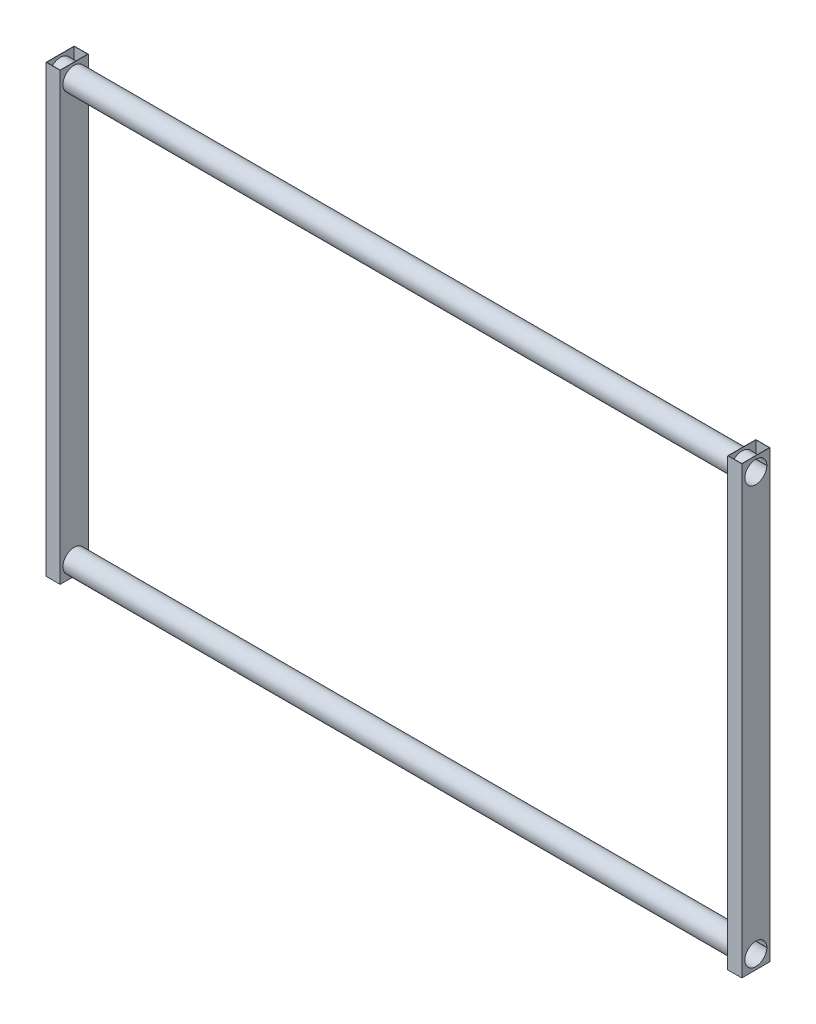
SolidWorks part; units mm, degrees
ref_plane "Front Plane" through (0, 0, 0) normal (0, 0, 1) x (1, 0, 0)
ref_plane "Top Plane" through (0, 0, 0) normal (0, 1, 0) x (1, 0, 0)
ref_plane "Right Plane" through (0, 0, 0) normal (1, 0, 0) x (0, 0, -1)
sketch "Sketch3" plane through (0, 0, 0) normal (0, 1, 0) x (1, 0, 0)
  line L0 (0, 209.8812) -> (0, -209.8812) construction
  line L2 (-209.8812, 0) -> (209.8812, 0) construction
  line L10 (2399, 209.8812) -> (2399, -209.8812) construction
  line L11 (1199.5, 209.8812) -> (1199.5, -209.8812) construction
  line L22 (-1, 49.5) -> (-49.5, 49.5)
  line L23 (0, 50.5) -> (-50.5, 50.5)
  line L24 (0, 50.5) -> (0, -50.5)
  line L25 (0, -50.5) -> (-50.5, -50.5)
  line L26 (-50.5, 50.5) -> (-50.5, -50.5)
  line L27 (-49.5, 49.5) -> (-49.5, -49.5)
  line L28 (-1, -49.5) -> (-49.5, -49.5)
  line L29 (-1, 49.5) -> (-1, -49.5)
  line L30 (2400, 49.5) -> (2400, -49.5)
  line L31 (2400, -49.5) -> (2448.5, -49.5)
  line L32 (2448.5, 49.5) -> (2448.5, -49.5)
  line L33 (2400, 49.5) -> (2448.5, 49.5)
  line L34 (2399, -50.5) -> (2449.5, -50.5)
  line L35 (2449.5, 50.5) -> (2449.5, -50.5)
  line L36 (2399, 50.5) -> (2449.5, 50.5)
  line L37 (2399, 50.5) -> (2399, -50.5)
  point P3 (0, 0)
  point P6 (0, 0)
  point P11 (0, 0)
  dimension "D1" = 101
  dimension "D2" = 50.5
  dimension "D3" = 1
  dimension "D7" = 2399
  dimension "D8" = 1199.5
extrude "Boss-Extrude1" add sketch "Sketch3" along normal blind 1600
sketch "Sketch4" plane through (2449.5, 0, 0) normal (1, 0, 0) x (0, 0, -1)
  circle A0 centre (0, 50) radius 39.5
  circle A1 centre (0, 1550) radius 39.5
  dimension "D1" = 79
  dimension "D3" = 79
  dimension "D2" = 50
  dimension "D4" = 1500
extrude "Cut-Extrude1" cut sketch "Sketch4" against normal up to surface (1 mm away) up to face at (2448.5, 800, 0)
sketch "Sketch5" plane through (-50.5, 0, 0) normal (-1, 0, 0) x (0, 0, 1)
  circle A0 centre (0, 50) radius 39.5
  circle A1 centre (0, 1550) radius 39.5
  dimension "D1" = 79
  dimension "D3" = 79
  dimension "D2" = 50
  dimension "D4" = 1500
extrude "Cut-Extrude2" cut sketch "Sketch5" against normal up to surface (1 mm away) up to face at (-49.5, 800, 0)
sketch "Sketch6" plane through (2400, 0, 0) normal (1, 0, 0) x (0, 0, -1)
  circle A0 centre (0, 50) radius 40.5
  circle A1 centre (0, 1550) radius 40.5
  dimension "D1" = 81
  dimension "D2" = 81
extrude "Cut-Extrude3" cut sketch "Sketch6" against normal up to surface (2401 mm away) up to face at (-1, 800, 0)
sketch "Sketch7" plane through (2448.5, 0, 0) normal (-1, 0, 0) x (0, 0, 1)
  line L0 (0, 50) -> (-75.3066, 50) construction
  line L1 (-39.4968, 50.5) -> (-40.4969, 50.5)
  line L2 (-39.4968, 49.5) -> (-40.4969, 49.5)
  line L3 (0, 1550) -> (-75.3066, 1550) construction
  line L6 (-367.27, 800) -> (289.7486, 800) construction
  line L7 (-40.4969, 1550.5) -> (-39.4968, 1550.5)
  line L8 (-40.4969, 1549.5) -> (-39.4968, 1549.5)
  arc A0 (-40.4969, 49.5) -> (-40.4969, 50.5) centre (0, 50) ccw
  arc A1 (-39.4968, 49.5) -> (-39.4968, 50.5) centre (0, 50) ccw
  circle A3 centre (0, 50) radius 40.5 construction
  circle A4 centre (0, 50) radius 39.5 construction
  arc A6 (-39.4968, 1550.5) -> (-39.4968, 1549.5) centre (0, 1550) cw
  arc A7 (-40.4969, 1550.5) -> (-40.4969, 1549.5) centre (0, 1550) cw
  point P1 (39.5, 50)
  point P9 (38.7303, 61.8411)
  dimension "D1" = 81
  dimension "D3" = 1
  dimension "D4" = 0.5
  dimension "D8" = 750
  dimension "D2" = 1
extrude "Boss-Extrude2" add sketch "Sketch7" along normal up to surface (2498 mm away) up to face at (-49.5, 50, -39.5)
